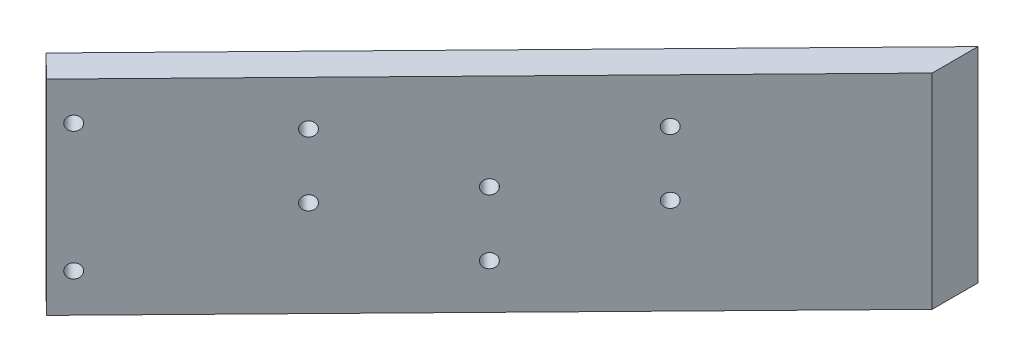
SolidWorks part; units mm, degrees
material "PEI"
ref_plane "Front Plane" through (0, 0, 0) normal (0, 0, 1) x (1, 0, 0)
ref_plane "Top Plane" through (0, 0, 0) normal (0, 1, 0) x (1, 0, 0)
ref_plane "Right Plane" through (0, 0, 0) normal (1, 0, 0) x (0, 0, -1)
sketch "Sketch1" plane through (0, 0, 0) normal (0, 1, 0) x (1, 0, 0)
  line L0 (0, 0) -> (0, 30)
  line L1 (0, 30) -> (83, 115)
  line L2 (0, 0) -> (18.2593, 0) construction
  line L3 (5, 27.9637) -> (5, -27.9637)
  line L5 (5, 27.9637) -> (83, 107.8432)
  line L6 (0, 0) -> (0.2825, 0) construction
  line L7 (5, 1.657) -> (5, 27.9637) construction
  line L8 (83, -115) -> (83, -107.8432)
  line L9 (83, 115) -> (83, 107.8432)
  line L10 (5, 27.9637) -> (86.5774, 111.5068) construction
  line L11 (5, -27.9637) -> (83, -107.8432)
  line L12 (0, -30) -> (83, -115)
  line L13 (0, 0) -> (0, -30)
  line L14 (5, 1.657) -> (5, 1.657) construction
  dimension "D1" = 30
  dimension "D2" = 83
  dimension "D4" = 85
  dimension "D3" = 5
extrude "Boss-Extrude1" add sketch "Sketch1" along normal blind 32
sketch "Sketch2" plane through (0, 32, 0) normal (0, 1, 0) x (1, 0, 0)
  line L0 (83, 115) -> (83, -115)
  line L1 (83, -115) -> (0, -30)
  line L2 (0, -30) -> (0, 30)
  line L3 (0, 30) -> (83, 115)
extrude "Boss-Extrude2" [suppressed] add sketch "Sketch2" along normal blind 5
fillet "Fillet1" radius 10 2 edges at (0, 16, -30) (0, 16, 30)
sketch "Sketch3" [suppressed] plane through (0, 37, 0) normal (0, 1, 0) x (1, 0, 0)
  line L0 (0, 25.9274) -> (0, -25.9274) construction
  line L1 (5, -30) -> (65, -30)
  line L2 (5, -30) -> (5, 30)
  line L3 (5, 30) -> (65, 30)
  line L4 (65, -30) -> (65, 30)
  line L5 (5, -30) -> (65, 30) construction
  line L6 (5, 30) -> (65, -30) construction
  point P0 (35, 0)
  dimension "D1" = 60
  dimension "D2" = 60
  dimension "D3" = 5
extrude "Cut-Extrude1" [suppressed] cut sketch "Sketch3" against normal through all
sketch "Sketch4" plane through (0, 32, 0) normal (0, 1, 0) x (1, 0, 0)
  line L4 (120.6904, -133.051) -> (-49.42, -133.051)
  line L6 (14.5774, -37.7719) -> (11, -41.2651) construction
  line L11 (83, -107.8432) -> (5, -27.9637) construction
  line L12 (2.8453, -32.9138) -> (83, -115) construction
  line L13 (14.5774, 37.7719) -> (11, 41.2651) construction
  line L14 (5, 27.9637) -> (83, 107.8432) construction
  line L15 (83, 115) -> (2.8453, 32.9138) construction
  line L16 (14.5774, -37.7719) -> (14.5774, 37.7719) construction
  line L17 (11, -41.2651) -> (0, -41.2651) construction
  line L18 (0, -41.2651) -> (0, 41.2651) construction
  line L19 (11, 41.2651) -> (0, 41.2651) construction
  line L20 (120.6904, -133.051) -> (120.6904, 124.9571)
  line L21 (120.6904, 124.9571) -> (-49.42, 124.9571)
  line L22 (-49.42, -133.051) -> (-49.42, 124.9571)
  line L25 (0, 0) -> (-50000, 0) construction
  line L26 (87.5774, 112.5309) -> (84, 116.0241)
  line L27 (14.5774, 37.7719) -> (87.5774, 112.5309)
  line L28 (84, 116.0241) -> (11, 41.2651)
  line L29 (14.5774, 37.7719) -> (11, 41.2651)
  dimension "D1" = 11
extrude "Cut-Extrude2" cut sketch "Sketch4" against normal through all
sketch "Sketch6" plane through (-14.9957, 0, -14.6429) normal (-0.7155, 0, -0.6986) x (-0.6986, 0, 0.7155)
  line L0 (-35.7778, 16) -> (-50035.7778, 16) construction
  line L1 (-37.2091, 0) -> (-37.2091, 32) construction
  circle A0 centre (-40.2091, 26) radius 1.1
  circle A1 centre (-40.2091, 6) radius 1.1
  point P6 (-37.2091, 16)
  dimension "D1" = 2.2
  dimension "D2" = 3
  dimension "D3" = 10
extrude "Cut-Extrude3" cut sketch "Sketch6" against normal through all
sketch "Sketch7" plane through (-11.4184, 0, -11.1497) normal (0.7155, 0, 0.6986) x (0.6986, 0, -0.7155)
  line L0 (86.1776, 0) -> (86.1776, 50000) construction
  line L1 (37.2091, 0) -> (135.1461, 0) construction
  line L2 (135.1461, 20) -> (-49864.8539, 20) construction
  line L5 (37.2091, 32) -> (135.1461, 32) construction
  line L6 (89.0438, 12) -> (-49910.9562, 12) construction
  circle A0 centre (66.1776, 15) radius 1.1
  circle A1 centre (66.1776, 25) radius 1.1
  circle A2 centre (106.1776, 25) radius 1.1
  circle A3 centre (106.1776, 15) radius 1.1
  circle A4 centre (86.1776, 17) radius 1.1
  circle A5 centre (86.1776, 7) radius 1.1
  point P4 (86.1776, 0)
  dimension "D3" = 2.2
  dimension "D1" = 5
  dimension "D2" = 20
  dimension "D4" = 15
  dimension "D5" = 15
  dimension "D6" = 5
extrude "Cut-Extrude4" cut sketch "Sketch7" against normal through all
